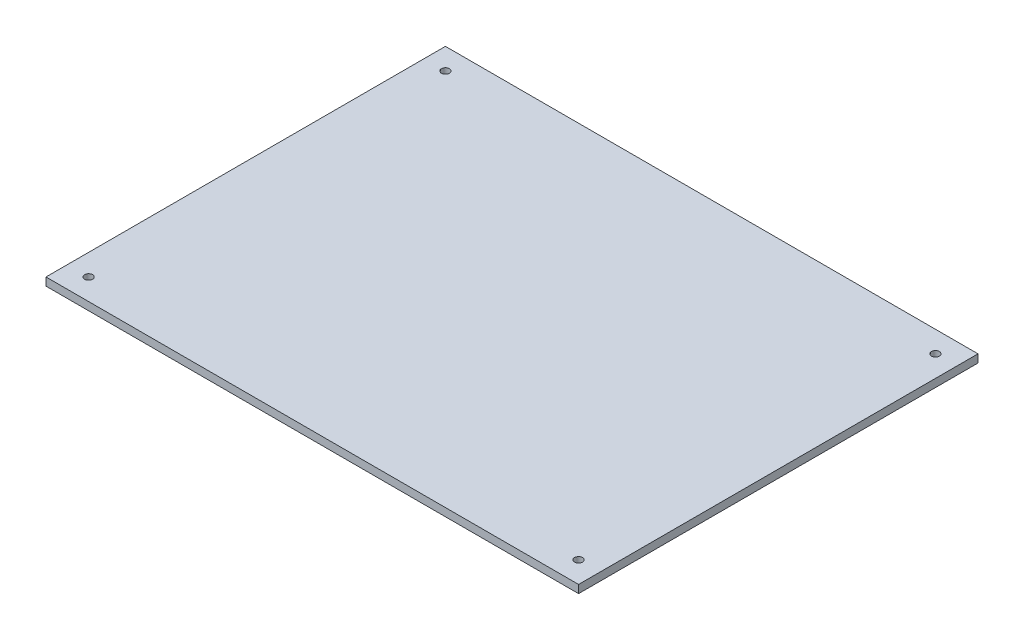
SolidWorks part; units mm, degrees
ref_plane "前基準面" through (0, 0, 0) normal (0, 0, 1) x (1, 0, 0)
ref_plane "上基準面" through (0, 0, 0) normal (0, 1, 0) x (1, 0, 0)
ref_plane "右基準面" through (0, 0, 0) normal (1, 0, 0) x (0, 0, -1)
sketch "草圖1" plane through (0, 0, 0) normal (0, 1, 0) x (1, 0, 0)
  line L1 (-104.0895, 83.5227) -> (95.9105, 83.5227)
  line L2 (-104.0895, 83.5227) -> (-104.0895, -66.4773)
  line L3 (-104.0895, -66.4773) -> (95.9105, -66.4773)
  line L4 (95.9105, 83.5227) -> (95.9105, -66.4773)
  circle A0 centre (-96.0895, 75.5227) radius 1.5
  circle A1 centre (-96.0895, -58.4773) radius 1.5
  circle A2 centre (87.9105, -58.4773) radius 1.5
  circle A3 centre (87.9105, 75.5227) radius 1.5
  dimension "D3" = 3
  dimension "D4" = 8
  dimension "D5" = 8
  dimension "D7" = 8
  dimension "D8" = 8
  dimension "D10" = 8
  dimension "D11" = 8
  dimension "D1" = 200
  dimension "D2" = 150
  dimension "D6" = 8
  dimension "D9" = 8
extrude "填料-伸長1" add sketch "草圖1" along normal blind 3
